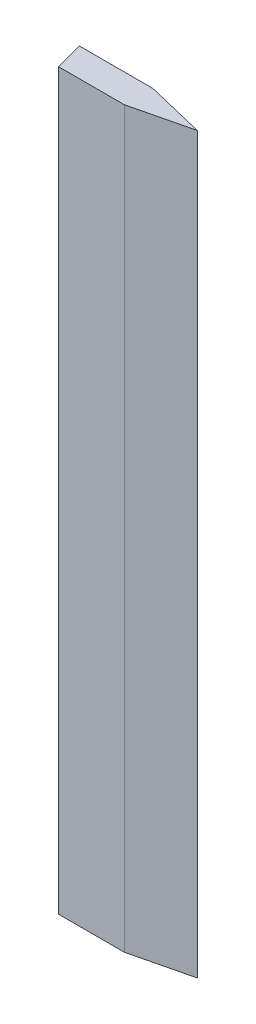
SolidWorks part; units mm, degrees
material "PS HI"
ref_plane "Front Plane" through (0, 0, 0) normal (0, 0, 1) x (1, 0, 0)
ref_plane "Top Plane" through (0, 0, 0) normal (0, 1, 0) x (1, 0, 0)
ref_plane "Right Plane" through (0, 0, 0) normal (1, 0, 0) x (0, 0, -1)
sketch "Sketch1" plane through (0, 0, 0) normal (0, 1, 0) x (1, 0, 0)
  line L0 (0, 0) -> (6.35, 0)
  line L1 (6.35, 0) -> (11.43, -1.2268)
  line L2 (11.43, -1.2268) -> (6.35, -2.4536)
  line L3 (6.35, -2.4536) -> (0.6575, -2.4536)
  line L4 (0.6575, -2.4536) -> (0, 0)
  line L5 (0, 0) -> (0, -2.8747) construction
  dimension "D1" = 6.35
  dimension "D2" = 5.08
  dimension "D3" = 5.08
  dimension "D4" = 1.2268
  dimension "D5" = 1.2268
  dimension "D6" = 15
extrude "Boss-Extrude1" add sketch "Sketch1" along normal blind 63.5
